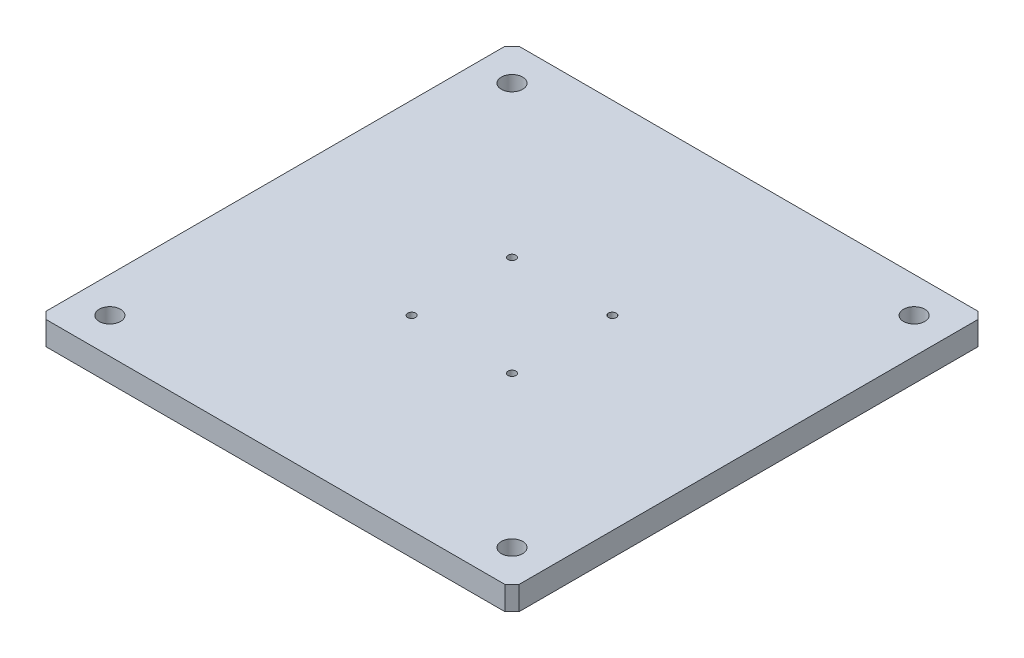
SolidWorks part; units mm, degrees
ref_plane "Front" through (0, 0, 0) normal (0, 0, 1) x (1, 0, 0)
ref_plane "Top" through (0, 0, 0) normal (0, 1, 0) x (1, 0, 0)
ref_plane "Right" through (0, 0, 0) normal (1, 0, 0) x (0, 0, -1)
sketch "Sketch1" plane through (0, 0, 0) normal (0, 1, 0) x (1, 0, 0)
  line L0 (100, 110.1618) -> (100, -115.3183) construction
  line L1 (-113.6776, 0) -> (114.1464, 0) construction
  line L3 (0, -100) -> (200, -100)
  line L4 (0, -100) -> (0, 100)
  line L5 (0, 100) -> (200, 100)
  line L6 (200, -100) -> (200, 100)
  dimension "D1" = 200
  dimension "D2" = 200
extrude "Boss-Extrude1" add sketch "Sketch1" along normal blind 10
hole_wizard "M8 Clearance Hole1" positions "Sketch3" profile "Sketch2" hole size "M8" standard "JIS" end condition through all
sketch "Sketch3" plane through (0, 10, 0) normal (0, 1, 0) x (-1, 0, 0)
  line L0 (0, -100) -> (0, 100) construction
  line L2 (14.239, 0) -> (-210.9855, 0) construction
  line L4 (-200, -100) -> (0, -100) construction
  line L5 (-200, 100) -> (-200, -100) construction
  line L7 (0, 100) -> (-200, 100) construction
  point P0 (-15, 85)
  point P1 (-15, -85)
  point P3 (-185, -85)
  point P5 (-185, 85)
  dimension "D1" = 170
  dimension "D2" = 15
  dimension "D3" = 15
  dimension "D4" = 170
  dimension "D5" = 15
  dimension "D6" = 15
sketch "Sketch2" plane through (15, 10, 85) normal (1, 0, 0) x (0, 0, 1)
  line L0 (0, 0) -> (0, 10)
  line L1 (0, 10) -> (4.5, 10)
  line L2 (4.5, 10) -> (4.5, 0)
  line L5 (4.5, 0) -> (0, 0)
  line L11 (0, -6.35) -> (0, 107.95) construction
  dimension "通し穴の直径" = 9
  dimension "通し穴の深さ" = 10
hole_wizard "M4x0.7 Tapped Hole1" positions "Sketch5" profile "Sketch4" tap size "M4x0.7" standard "JIS" end condition through all
sketch "Sketch5" plane through (0, 10, 0) normal (0, 1, 0) x (-1, 0, 0)
  line L0 (14.9658, 0) -> (-208.9969, 0) construction
  line L3 (-100, 41.9119) -> (-100, -46.5832) construction
  line L6 (-71.2127, 28.7873) -> (-131.9873, -31.9873) construction
  line L9 (-126.9593, 26.9593) -> (-70.0798, -29.9202) construction
  line L12 (0, -100) -> (0, 100) construction
  circle A0 centre (-100, 0) radius 30 construction
  point P0 (-78.7868, 21.2132)
  point P1 (-121.2132, 21.2132)
  point P3 (-121.2132, -21.2132)
  point P5 (-78.7868, -21.2132)
  dimension "D1" = 60
  dimension "D2" = 100
  dimension "D3" = 45
  dimension "D4" = 45
sketch "Sketch4" plane through (78.7868, 10, 21.2132) normal (1, 0, 0) x (0, 0, 1)
  line L0 (0, 0) -> (0, 10)
  line L1 (0, 10) -> (1.65, 10)
  line L2 (1.65, 10) -> (1.65, 0)
  line L5 (1.65, 0) -> (0, 0)
  line L11 (0, -6.35) -> (0, 107.95) construction
  dimension "次ｻｰﾌｪｽまでのねじ下穴ﾄﾞﾘﾙ直径" = 3.3
  dimension "次ｻｰﾌｪｽまでのねじ下穴ﾄﾞﾘﾙの深さ" = 10
cosmetic thread "Hole Thread1" parameters "D2"=4
cosmetic thread "Hole Thread2" parameters "D2"=4
cosmetic thread "Hole Thread3" parameters "D2"=4
cosmetic thread "Hole Thread4" parameters "D2"=4
chamfer "Chamfer1" distance 3 angle 45 4 edges at (0, 5, -100) (200, 5, -100) (0, 5, 100) (200, 5, 100)
